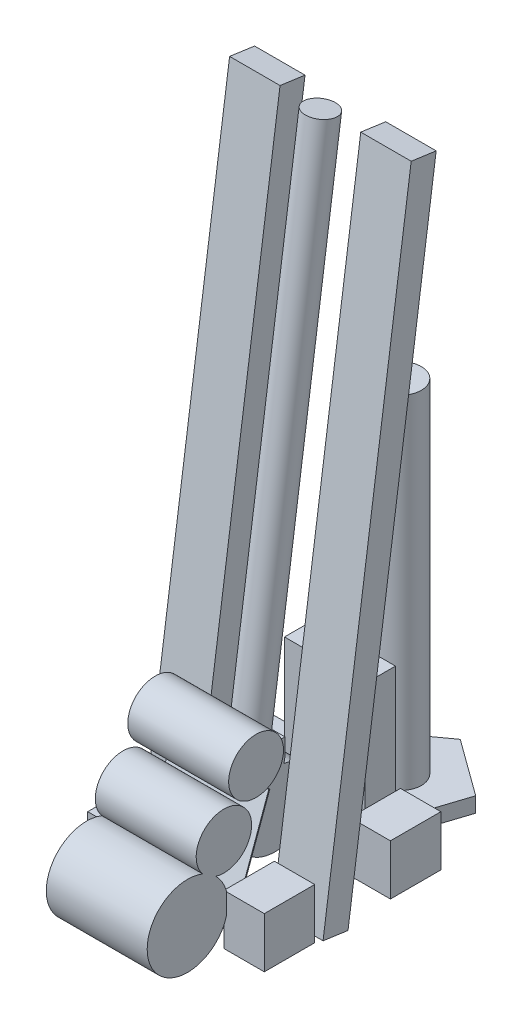
SolidWorks part; units mm, degrees
ref_plane "Front Plane" through (0, 0, 0) normal (0, 0, 1) x (1, 0, 0)
ref_plane "Top Plane" through (0, 0, 0) normal (0, 1, 0) x (1, 0, 0)
ref_plane "Right Plane" through (0, 0, 0) normal (1, 0, 0) x (0, 0, -1)
sketch3d "Bounding Box"
  line L0 (-228.6, 0, 228.6) -> (-228.6, 457.2, 228.6)
  line L1 (228.6, 0, 228.6) -> (228.6, 0, -228.6)
  line L2 (228.6, 0, 228.6) -> (-228.6, 0, 228.6)
  line L3 (-228.6, 0, 228.6) -> (-228.6, 0, -228.6)
  line L4 (228.6, 0, -228.6) -> (-228.6, 0, -228.6)
  line L5 (228.6, 0, 228.6) -> (-228.6, 0, -228.6) construction
  line L6 (-228.6, 0, 228.6) -> (228.6, 0, -228.6) construction
  line L7 (-228.6, 0, -228.6) -> (-228.6, 457.2, -228.6)
  line L8 (228.6, 0, -228.6) -> (228.6, 457.2, -228.6)
  line L9 (-228.6, 457.2, -228.6) -> (228.6, 457.2, -228.6)
  line L10 (228.6, 0, 228.6) -> (228.6, 457.2, 228.6)
  line L11 (228.6, 457.2, 228.6) -> (-228.6, 457.2, 228.6)
  line L12 (-228.6, 457.2, 228.6) -> (-228.6, 456.9018, 228.6)
  line L13 (228.6, 457.2, -228.6) -> (228.6, 457.2, 228.6)
  line L14 (-228.6, 457.2, -228.6) -> (-228.6, 456.9018, 228.6)
  point P0 (0, 0, 0)
  dimension "D1" = 457.2
sketch "Sketch1" plane through (0, 0, 0) normal (0, 1, 0) x (1, 0, 0)
  line L0 (-222.25, 222.25) -> (222.25, -222.25) construction
  line L1 (-222.25, -222.25) -> (-120.65, -222.25)
  line L2 (-222.25, -222.25) -> (-222.25, -95.25)
  line L3 (-222.25, -95.25) -> (-120.65, -95.25)
  line L4 (-120.65, -222.25) -> (-120.65, -95.25)
  line L5 (120.65, -222.25) -> (222.25, -222.25)
  line L6 (120.65, -222.25) -> (120.65, -95.25)
  line L7 (120.65, -95.25) -> (222.25, -95.25)
  line L8 (222.25, -222.25) -> (222.25, -95.25)
  line L9 (222.25, 95.25) -> (120.65, 95.25)
  line L10 (222.25, 95.25) -> (222.25, 222.25)
  line L11 (222.25, 222.25) -> (120.65, 222.25)
  line L12 (120.65, 95.25) -> (120.65, 222.25)
  line L13 (-222.25, 222.25) -> (-120.65, 222.25)
  line L14 (-222.25, 222.25) -> (-222.25, 95.25)
  line L15 (-222.25, 95.25) -> (-120.65, 95.25)
  line L16 (-120.65, 222.25) -> (-120.65, 95.25)
  dimension "D1" = 444.5
  dimension "D2" = 444.5
  dimension "D3" = 101.6
  dimension "D4" = 127
extrude "Drivetrain" add sketch "Sketch1" along normal blind 127 contours L14 L15 L16 L13 | L3 L4 L1 L2 | L7 L8 L5 L6 | L9 L12 L11 L10
sketch "Sketch3" plane through (0, 0, 0) normal (0, 1, 0) x (1, 0, 0)
  line L0 (0, 0) -> (0, 343.4529) construction
  line L1 (-88.0591, 222.25) -> (88.0591, 222.25)
  line L2 (88.0591, 222.25) -> (142.4826, 389.7483)
  line L3 (142.4826, 389.7483) -> (0, 493.268)
  line L4 (0, 493.268) -> (-142.4826, 389.7483)
  line L5 (-142.4826, 389.7483) -> (-88.0591, 222.25)
  line L6 (-222.25, 222.25) -> (-120.65, 222.25) construction
  circle A0 centre (0, 343.4529) radius 121.2029 construction
  dimension "D1" = 271.018
extrude "Boss-Extrude2" add sketch "Sketch3" along normal blind 38.1 separate body
sketch "Sketch4" plane through (0, 38.1, 0) normal (0, 1, 0) x (1, 0, 0)
  circle A0 centre (0, 343.4529) radius 51.816
  dimension "D1" = 103.632
extrude "Boss-Extrude3" add sketch "Sketch4" along normal blind 861.822
sketch "Sketch5" plane through (0, 0, 0) normal (1, 0, 0) x (0, 0, -1)
  line L0 (-40.2383, 289.6932) -> (141.2298, 1588.8551) construction
  line L1 (343.4529, 1270) -> (343.4529, 1574.8) construction
  line L2 (395.2689, 899.922) -> (291.6369, 899.922) construction
  line L5 (26.4367, 289.6932) -> (-106.9133, 289.6932)
  line L6 (-106.9133, 289.6932) -> (-106.9133, 179.4312)
  line L7 (26.4367, 246.4116) -> (26.4367, 289.6932)
  line L8 (-95.25, 50.8) -> (95.25, 50.8) construction
  line L9 (-95.25, 127) -> (-95.25, 0) construction
  line L10 (95.25, 127) -> (95.25, 0) construction
  arc A0 (343.4529, 1574.8) -> (141.2298, 1588.8551) centre (241.8529, 1574.8) ccw construction
  spline S0 degree 3 poles (-106.9133, 179.4312) (-106.9223, 177.3141) (-106.8447, 173.1) (-106.3116, 164.5179) (-104.9379, 153.6652) (-102.1471, 140.5584) (-96.8607, 123.2075) (-89.1402, 106.3802) (-78.6958, 90.8789) (-69.4081, 80.1671) (-60.3862, 72.2456) (-52.3913, 66.6913) (-45.9915, 62.9549) (-39.2789, 59.7365) (-30.066, 56.1618) (-18.1181, 52.9777) (-3.3907, 51.1393) (11.4705, 51.2575) (26.2088, 53.3587) (40.5525, 57.5279) (54.195, 63.8748) (66.7209, 72.6366) (77.2797, 83.231) (85.9292, 95.2718) (92.6114, 108.4326) (97.2981, 122.4363) (99.9199, 137.027) (100.3856, 151.8955) (98.5438, 166.7592) (94.8874, 178.8595) (90.5531, 188.1375) (85.2184, 197.0379) (77.081, 206.8457) (65.5294, 216.5615) (52.6359, 224.2044) (38.7586, 229.7489) (29.0198, 231.9863) (24.1027, 232.7077) knots 0.074418 0.074418 0.074418 0.074418 0.088879 0.103339 0.13226 0.161182 0.190103 0.247945 0.276866 0.305788 0.334709 0.349169 0.36363 0.378091 0.392551 0.421472 0.450394 0.479315 0.508236 0.537157 0.566078 0.595 0.623921 0.652842 0.681763 0.710684 0.739606 0.768527 0.797448 0.826369 0.84083 0.85529 0.884212 0.913133 0.942054 0.970975 0.999896 0.999896 0.999896 0.999896
  spline S1 degree 3 poles (24.1027, 232.7077) (24.3828, 233.8376) (24.8969, 236.1027) (25.4367, 238.9867) (25.8068, 241.319) (26.0126, 242.7843) (26.163, 243.9699) (26.2491, 244.697) (26.3182, 245.3181) (26.3704, 245.8022) (26.4103, 246.1683) (26.4367, 246.4116) knots -0.022895 -0.022895 -0.022895 -0.022895 0.042323 0.10754 0.140149 0.172758 0.189063 0.205367 0.213519 0.221671 0.237976 0.237976 0.237976 0.237976
  point P1 (343.4529, 899.922)
  dimension "D3" = 101.6
  dimension "D1" = 1270
  dimension "D2" = 304.8
extrude "Boss-Extrude4" add sketch "Sketch5" along normal mid plane 50.8 separate body contours L5 L6 S0 S1 L7
ref_plane "Plane1" through (0, 11.0569, 79.1584) normal (0, -0.1383, -0.9904) x (0, 0.9904, -0.1383)
sketch "Sketch7" plane through (0, 11.0569, 79.1584) normal (0, -0.1383, -0.9904) x (0, 0.9904, -0.1383)
  line L0 (1593.1159, 0) -> (272.1176, 0)
  line L1 (1593.1159, 0) -> (1593.1159, 38.1)
  line L2 (1593.1159, 38.1) -> (272.1176, 38.1)
  line L3 (272.1176, 38.1) -> (272.1176, 0)
  dimension "D1" = 38.1
revolve "Revolve1" add sketch "Sketch7" angle 360 about L0
sketch "Sketch8" plane through (-120.65, 0, 0) normal (1, 0, 0) x (0, 0, -1)
  line L0 (-106.9133, 289.6932) -> (-187.8765, 67.2486)
  line L1 (-222.25, 127) -> (-222.25, 0) construction
  line L2 (-222.25, 0) -> (-95.25, 0) construction
  line L3 (-1229.5961, 43.18) -> (48770.4039, 43.18) construction
  line L4 (-109.3001, 290.5619) -> (-190.2633, 68.1173)
  line L5 (-109.3001, 290.5619) -> (-106.9133, 289.6932)
  line L6 (-222.25, 45.72) -> (-222.25, 43.18)
  arc A0 (-187.8765, 67.2486) -> (-222.25, 43.18) centre (-222.25, 79.7595) cw
  arc A1 (-190.2633, 68.1173) -> (-222.25, 45.72) centre (-222.25, 79.7595) cw
  dimension "D1" = 43.18
  dimension "D2" = 70
  dimension "D3" = 2.54
extrude "Boss-Extrude5" add sketch "Sketch8" along normal blind 241.3 separate body
sketch "Sketch12" plane through (0, 0, 0) normal (1, 0, 0) x (0, 0, -1)
  line L0 (-320.2572, 101.6) -> (-147.7157, 364.1305) construction
  circle A0 centre (-320.2572, 101.6) radius 101.6
  circle A1 centre (-228.7268, 240.868) radius 69.7607
  circle A2 centre (-147.7157, 364.1305) radius 69.014
  dimension "D2" = 203.2
  dimension "D1" = 101.6
extrude "Boss-Extrude8" add sketch "Sketch12" along normal mid plane 254 separate body
sketch "Sketch9" plane through (0, 11.0569, 79.1584) normal (0, -0.1383, -0.9904) x (0, 0.9904, -0.1383)
  line L0 (1593.1159, -38.1) -> (1593.1159, 38.1) construction
  line L1 (1593.1159, 101.6) -> (-11.1643, 101.6)
  line L2 (1593.1159, 101.6) -> (1593.1159, 228.6)
  line L3 (1593.1159, 228.6) -> (-11.1643, 228.6)
  line L4 (-11.1643, 101.6) -> (-11.1643, 228.6)
  line L5 (1593.1159, -228.6) -> (-11.1643, -228.6)
  line L6 (1593.1159, -228.6) -> (1593.1159, -101.6)
  line L7 (1593.1159, -101.6) -> (-11.1643, -101.6)
  line L8 (-11.1643, -228.6) -> (-11.1643, -101.6)
  dimension "D1" = 127
extrude "Lift" add sketch "Sketch9" along normal blind 63.5 separate body
sketch "Sketch10" plane through (0, 0, 0) normal (0, 1, 0) x (1, 0, 0)
  line L0 (228.6, 228.6) -> (-228.6, 228.6) construction
  line L1 (-101.6, 228.6) -> (101.6, 228.6)
  line L2 (-101.6, 228.6) -> (-101.6, 152.4)
  line L3 (-101.6, 152.4) -> (101.6, 152.4)
  line L4 (101.6, 228.6) -> (101.6, 152.4)
  line L5 (0, 0) -> (0, 152.4) construction
  line L6 (228.6, -228.6) -> (-228.6, 228.6) construction
  dimension "D1" = 203.2
  dimension "D2" = 76.2
extrude "Goal Lift" add sketch "Sketch10" along normal blind 381 separate body
